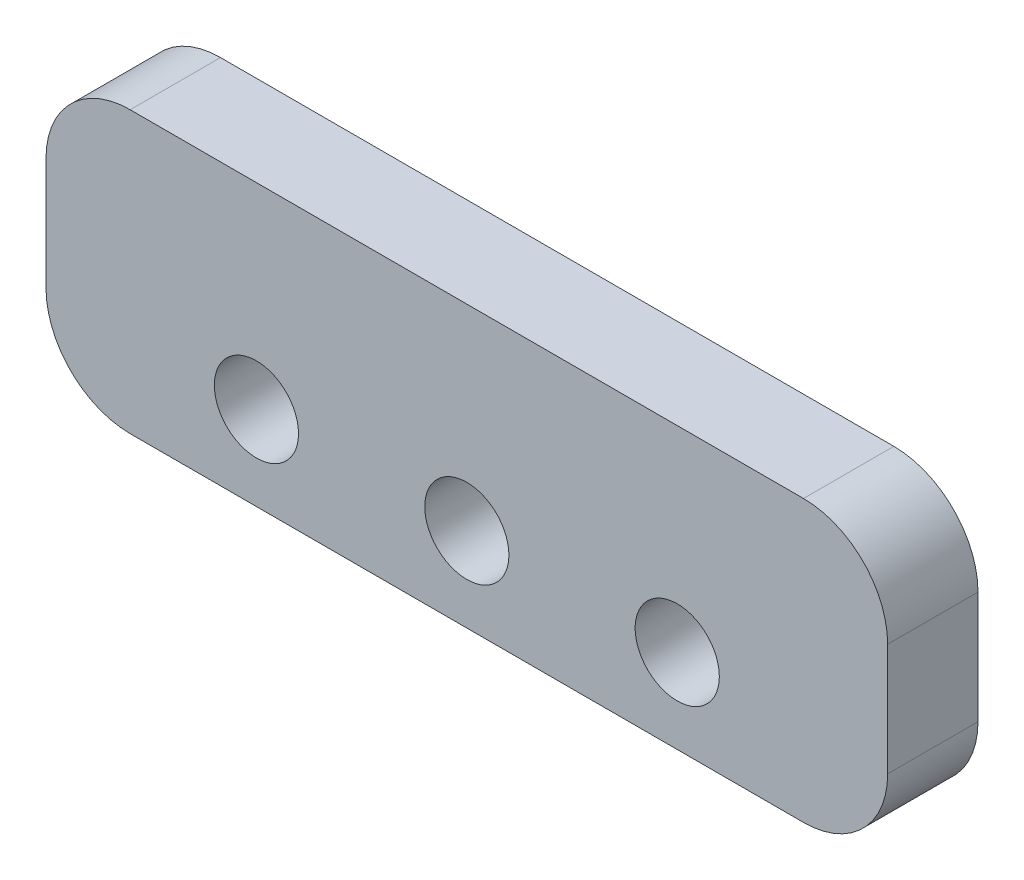
SolidWorks part; units mm, degrees
ref_plane "Front Plane" through (0, 0, 0) normal (0, 0, 1) x (1, 0, 0)
ref_plane "Top Plane" through (0, 0, 0) normal (0, 1, 0) x (1, 0, 0)
ref_plane "Right Plane" through (0, 0, 0) normal (1, 0, 0) x (0, 0, -1)
sketch "Sketch1" plane through (0, 0, 0) normal (0, 0, 1) x (1, 0, 0)
  line L0 (15, -3) -> (-15, -3)
  line L1 (-15, -3) -> (-15, 7)
  line L2 (-15, 7) -> (15, 7)
  line L3 (15, 7) -> (15, -3)
  line L5 (-15, 0) -> (-7.5, 0) construction
  line L6 (-7.5, 0) -> (0, 0) construction
  line L7 (0, 0) -> (7.5, 0) construction
  line L8 (7.5, 0) -> (15, 0) construction
  circle A0 centre (-7.5, 0) radius 1.5
  circle A1 centre (0, 0) radius 1.5
  circle A2 centre (7.5, 0) radius 1.5
  point P0 (0, 0)
  point P15 (0, 0)
  dimension "D3" = 3
  dimension "D1" = 10
  dimension "D2" = 30
  dimension "D4" = 3
extrude "Boss-Extrude1" add sketch "Sketch1" along normal mid plane 3.22
fillet "Fillet1" radius 3 4 edges at (15, -3, 0) (15, 7, 0) (-15, -3, 0) (-15, 7, 0)
